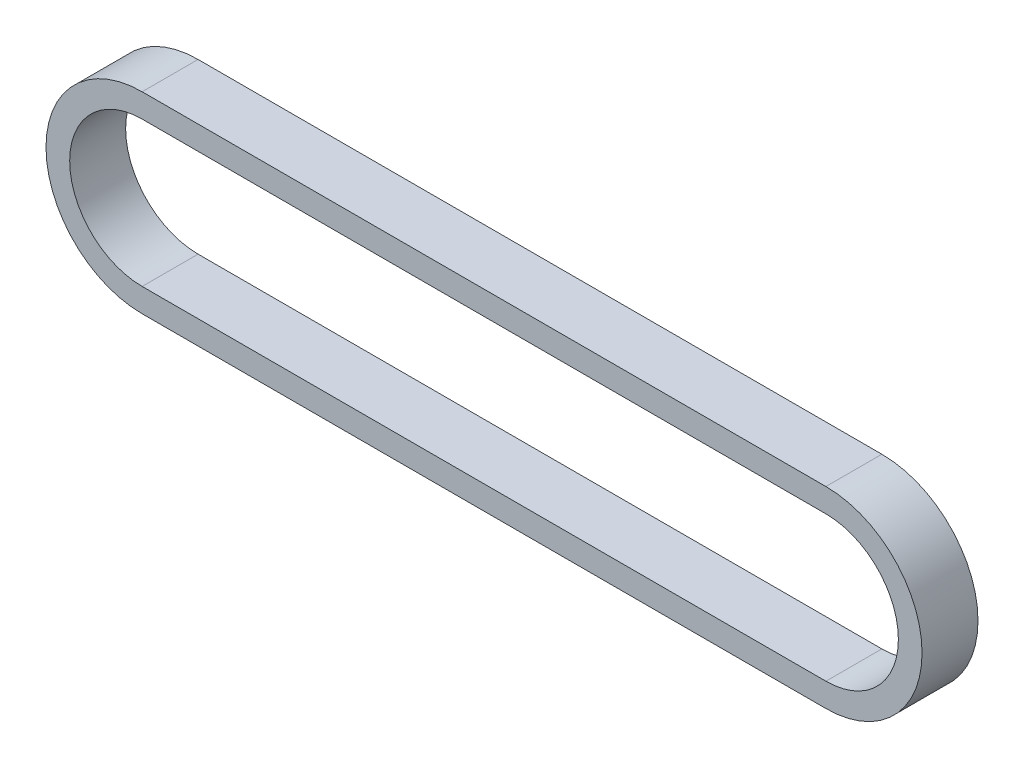
SolidWorks part; units mm, degrees
ref_plane "Front Plane" through (0, 0, 0) normal (0, 0, 1) x (1, 0, 0)
ref_plane "Top Plane" through (0, 0, 0) normal (0, 1, 0) x (1, 0, 0)
ref_plane "Right Plane" through (0, 0, 0) normal (1, 0, 0) x (0, 0, -1)
sketch "Sketch1" plane through (0, 0, 0) normal (0, 0, 1) x (1, 0, 0)
  line L0 (0, 14.324) -> (110, 14.324)
  line L1 (0, -14.324) -> (110, -14.324)
  line L2 (0, 0) -> (110, 0) construction
  arc A0 (0, 14.324) -> (0, -14.324) centre (0, 0) ccw
  arc A1 (110, -14.324) -> (110, 14.324) centre (110, 0) ccw
  dimension "D2" = 28.6479
  dimension "D3" = 28.6479
  dimension "D1" = 110
extrude "Extrude-Thin1" add sketch "Sketch1" along normal mid plane 9 thin thin type two direction wall 1.143 second wall 2.667
equation "\"Center Distance\"= 110mm"
equation "\"D1@Sketch1\"=\"Center Distance\""
equation "\"Pitch\"= 5mm"
equation "\"T1\"= 18"
equation "\"T2\"= 18"
equation "\"D2@Sketch1\" = \"Pitch\" * \"T1\" / 3.14159"
equation "\"D3@Sketch1\" = \"Pitch\" * \"T2\" / 3.14159"
equation "\"Teeth\"= 2 * \"Center Distance\" / \"Pitch\" + ( \"T1\" + \"T2\" ) / 2 + ( ( \"T2\" - \"T1\" ) / ( 2 * 3.14159 ) ) ^ 2 * \"Pitch\" / \"Center Distance\""
